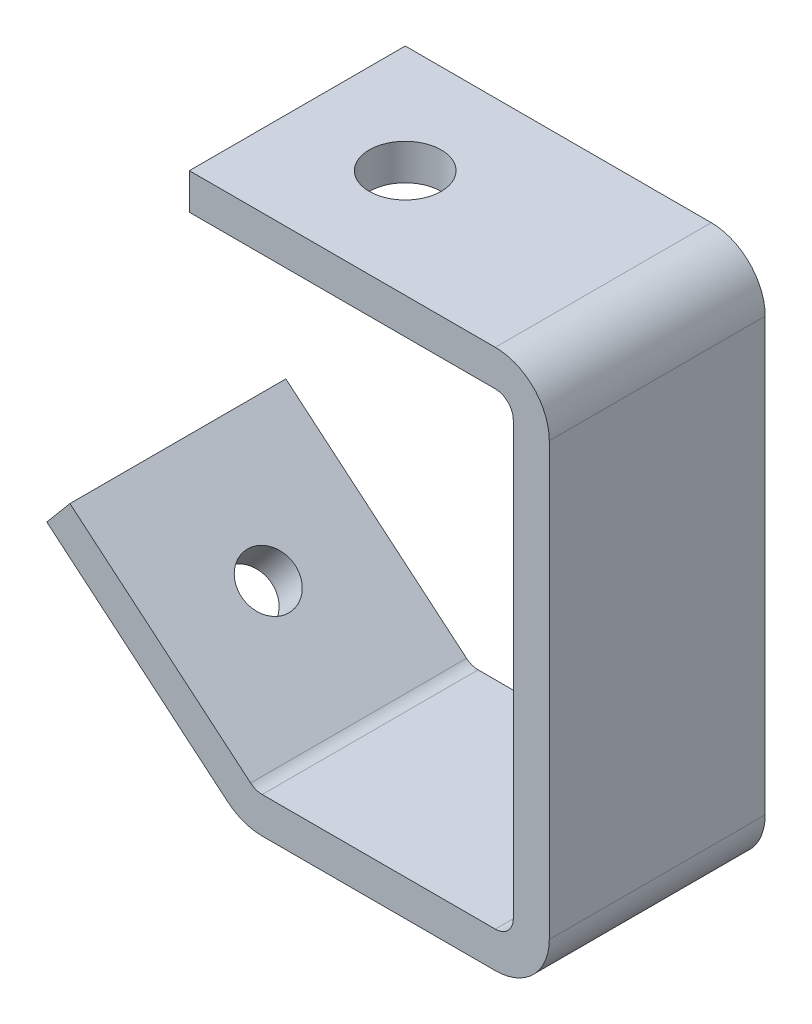
SolidWorks part; units mm, degrees
ref_plane "Front Plane" through (0, 0, 0) normal (0, 0, 1) x (1, 0, 0)
ref_plane "Top Plane" through (0, 0, 0) normal (0, 1, 0) x (1, 0, 0)
ref_plane "Right Plane" through (0, 0, 0) normal (1, 0, 0) x (0, 0, -1)
sketch "Sketch1" plane through (0, 0, 0) normal (0, 0, 1) x (1, 0, 0)
  line L0 (-133.5754, 0) -> (127.0939, 0) construction
  line L1 (-56.7771, -45.3954) -> (-88.6609, -18.6417)
  line L2 (-63.51, 47.625) -> (-9.52, 47.625)
  line L4 (-50.6514, -47.625) -> (-9.52, -47.625)
  line L5 (0, 38.105) -> (0, -38.105)
  arc A0 (0, 38.105) -> (-9.52, 47.625) centre (-9.52, 38.105) ccw
  arc A1 (-9.52, -47.625) -> (0, -38.105) centre (-9.52, -38.105) ccw
  arc A2 (-56.7771, -45.3954) -> (-50.6514, -47.625) centre (-50.6514, -38.095) ccw
  point P10 (0, 47.625)
  point P13 (0, -47.625)
  point P14 (0, 0)
  point P17 (-54.12, -47.625)
  dimension "D6" = 9.52
  dimension "D7" = 9.53
  dimension "D1" = 95.25
  dimension "D2" = 63.51
  dimension "D3" = 140
  dimension "D4" = 45.09
  dimension "D5" = 54.12
extrude "Extrude-Thin1" add sketch "Sketch1" along normal blind 38.1 thin
hole_wizard "Ø10.0mm Dowel Hole1" positions "Sketch3" profile "Sketch4" hole size "Ø10.0" standard "ISO"
sketch "Sketch3" plane through (0, 47.625, 0) normal (0, 1, 0) x (1, 0, 0)
  line L0 (-63.51, -38.1) -> (-63.51, 0) construction
  line L1 (-63.51, 0) -> (-9.52, 0) construction
  point P0 (-44.47, -19.05)
  dimension "D1" = 19.04
  dimension "D2" = 19.05
sketch "Sketch4" plane through (-44.47, 47.625, 19.05) normal (1, 0, 0) x (0, 0, 1)
  line L0 (0, 0) -> (0, 10.1655)
  line L1 (0, 10.1655) -> (6.35, 6.35)
  line L2 (6.35, 6.35) -> (6.35, 0)
  line L5 (6.35, 0) -> (0, 0)
  line L10 (0, 10.1655) -> (-6.35, 6.35) construction
  line L11 (0, -6.35) -> (0, 107.95) construction
  dimension "Hole Dia." = 12.7
  dimension "Hole Depth" = 6.35
  dimension "Drill Angle" = 118
hole_wizard "Ø10.0mm Dowel Hole2" positions "Sketch9" profile "Sketch8" hole size "Ø10.0" standard "ISO"
sketch "Sketch9" plane through (-45.8118, -54.5964, 0) normal (-0.6428, -0.766, 0) x (-0.766, 0.6428, 0)
  line L0 (14.3142, 0) -> (55.9356, 0) construction
  line L1 (55.9356, -38.1) -> (55.9356, 0) construction
  point P0 (35.1256, -19.05)
  dimension "D1" = 19.05
  dimension "D2" = 20.81
sketch "Sketch8" plane through (-72.7196, -32.0181, 19.05) normal (0, 0, 1) x (0.766, -0.6428, 0)
  line L0 (0, 0) -> (0, 9.2131)
  line L1 (0, 9.2131) -> (4.765, 6.35)
  line L2 (4.765, 6.35) -> (4.765, 0)
  line L5 (4.765, 0) -> (0, 0)
  line L10 (0, 9.2131) -> (-4.765, 6.35) construction
  line L11 (0, -6.35) -> (0, 107.95) construction
  dimension "Hole Dia." = 9.53
  dimension "Hole Depth" = 6.35
  dimension "Drill Angle" = 118
